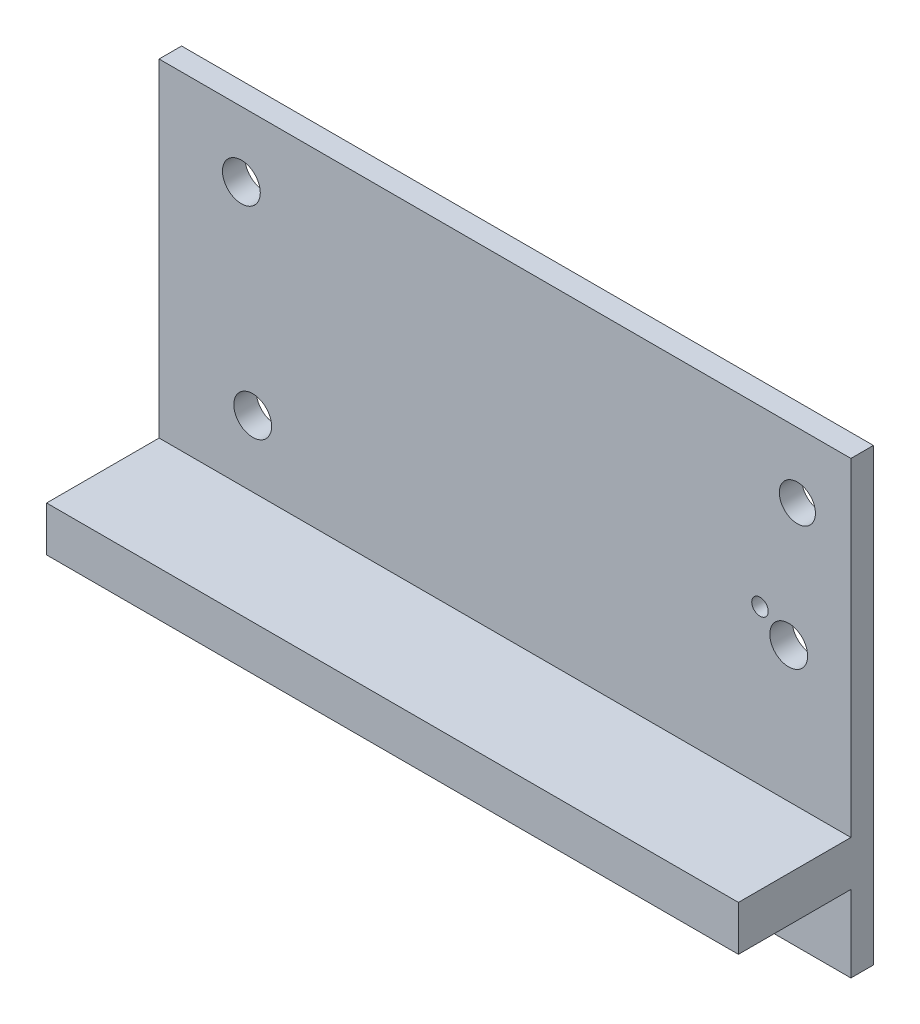
SolidWorks part; units mm, degrees
ref_plane "Plan de face" through (0, 0, 0) normal (0, 0, 1) x (1, 0, 0)
ref_plane "Plan de dessus" through (0, 0, 0) normal (0, 1, 0) x (1, 0, 0)
ref_plane "Plan de droite" through (0, 0, 0) normal (1, 0, 0) x (0, 0, -1)
sketch "Esquisse14" plane through (0, 0, 0) normal (0, 0, 1) x (1, 0, 0)
  line L0 (83.2018, -28.865) -> (21.7033, -28.865)
  line L1 (83.2018, -28.865) -> (83.2018, -68.865)
  line L2 (83.2018, -68.865) -> (21.7033, -68.865)
  line L3 (21.7033, -28.865) -> (21.7033, -68.865)
  circle A0 centre (78.4431, -34.6698) radius 1.6056
  circle A1 centre (77.6721, -46.0004) radius 1.6804
  circle A2 centre (29.0182, -34.6698) radius 1.6804
  circle A3 centre (30.0265, -52.1489) radius 1.6804
  circle A4 centre (75.1189, -44.32) radius 0.7331
  dimension "D1" = 40
extrude "Boss.-Extru.1" add sketch "Esquisse14" against normal blind 2
sketch "Esquisse15" plane through (0, 0, 0) normal (0, 0, 1) x (1, 0, 0)
  line L0 (83.2018, -62.045) -> (21.7033, -62.045) construction
  line L1 (83.2018, -68.865) -> (83.2018, -28.865) construction
  line L2 (21.7033, -28.865) -> (21.7033, -68.865) construction
  line L3 (21.7033, -68.865) -> (83.2018, -68.865) construction
  line L5 (21.7033, -62.045) -> (83.2018, -62.045)
  line L6 (21.7033, -62.045) -> (21.7033, -58.045)
  line L7 (21.7033, -58.045) -> (83.2018, -58.045)
  line L8 (83.2018, -62.045) -> (83.2018, -58.045)
  dimension "D1" = 6.82
  dimension "D2" = 4
extrude "Boss.-Extru.2" add sketch "Esquisse15" along normal blind 10
